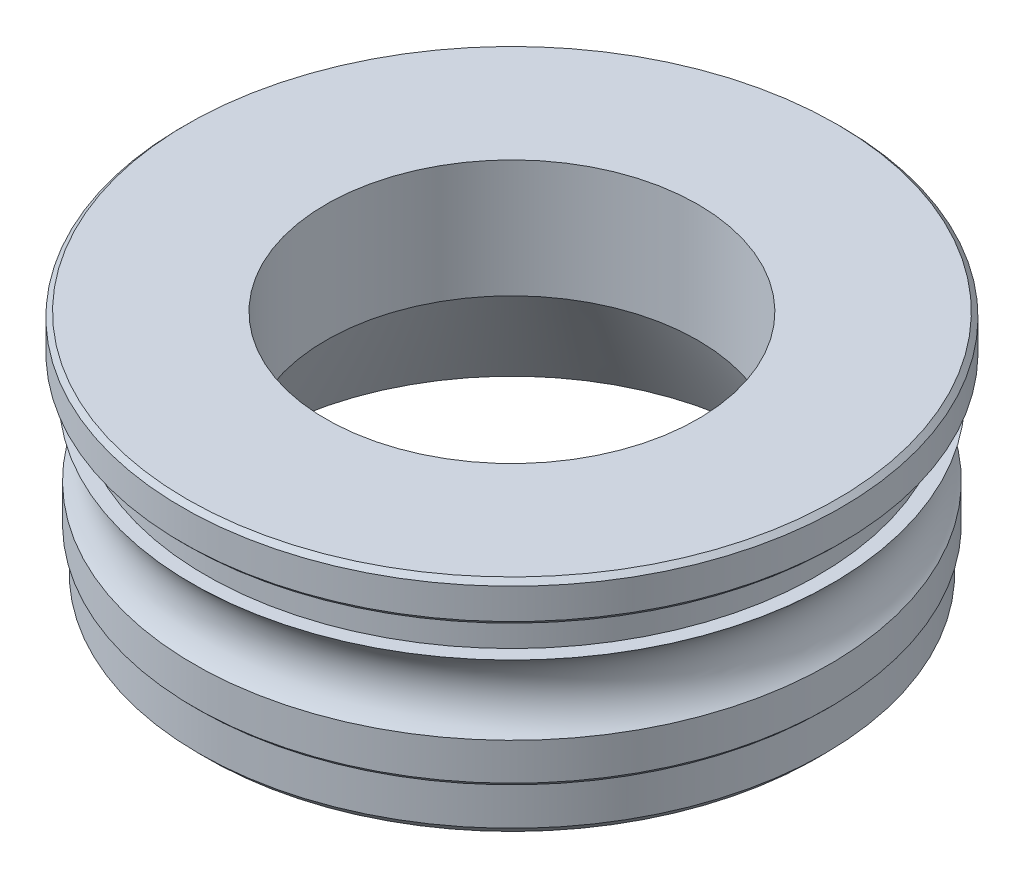
SolidWorks part; units mm, degrees
material "latón"
ref_plane "Alzado" through (0, 0, 0) normal (0, 0, 1) x (1, 0, 0)
ref_plane "Planta" through (0, 0, 0) normal (0, 1, 0) x (1, 0, 0)
ref_plane "Vista lateral" through (0, 0, 0) normal (1, 0, 0) x (0, 0, -1)
sketch "Croquis1" plane through (0, 0, 0) normal (0, 0, 1) x (1, 0, 0)
  line L0 (0, 0) -> (0, 5) construction
  line L1 (6.45, 0) -> (6.65, 0.2)
  line L2 (6.65, 0.2) -> (6.65, 1)
  line L3 (6.65, 1) -> (6.75, 1.1)
  line L4 (6.75, 1.1) -> (6.75, 1.767)
  line L5 (6.75, 1.767) -> (6.75, 1.889)
  line L6 (5.3934, 0) -> (6.45, 0)
  line L7 (3.95, 5) -> (6.9, 5)
  line L8 (6.9, 5) -> (7, 4.9)
  line L9 (7, 4.25) -> (6.9, 4.15)
  line L10 (6.5, 4.15) -> (6.5, 3.4)
  line L11 (6.5, 3.4) -> (6.8, 3.4)
  line L12 (3.95, 5) -> (3.95, 2.5)
  line L13 (3.95, 2.5) -> (5.3934, 0)
  line L14 (7, 4.9) -> (7, 4.25)
  line L15 (6.9, 4.15) -> (6.5, 4.15)
  arc A0 (6.75, 1.889) -> (6.8, 3.4) centre (7.4293, 2.6228) cw
  point P9 (7, 5)
  point P12 (7, 4.15)
  dimension "D9" = 5
  dimension "D8" = 1
  dimension "D10" = 3.05
  dimension "D2" = 0.2
  dimension "D3" = 7.9
  dimension "D4" = 0.8
  dimension "D5" = 0.1
  dimension "D6" = 6.45
  dimension "D7" = 45
  dimension "D11" = 6.5
  dimension "D12" = 2.5
  dimension "D14" = 0.3
  dimension "D15" = 0.122
  dimension "D16" = 30
  dimension "D17" = 3.4
  dimension "D18" = 1.767
  dimension "D19" = 0.85
  dimension "D20" = 0.25
revolve "Revolución1" add sketch "Croquis1" angle 360 about L0
